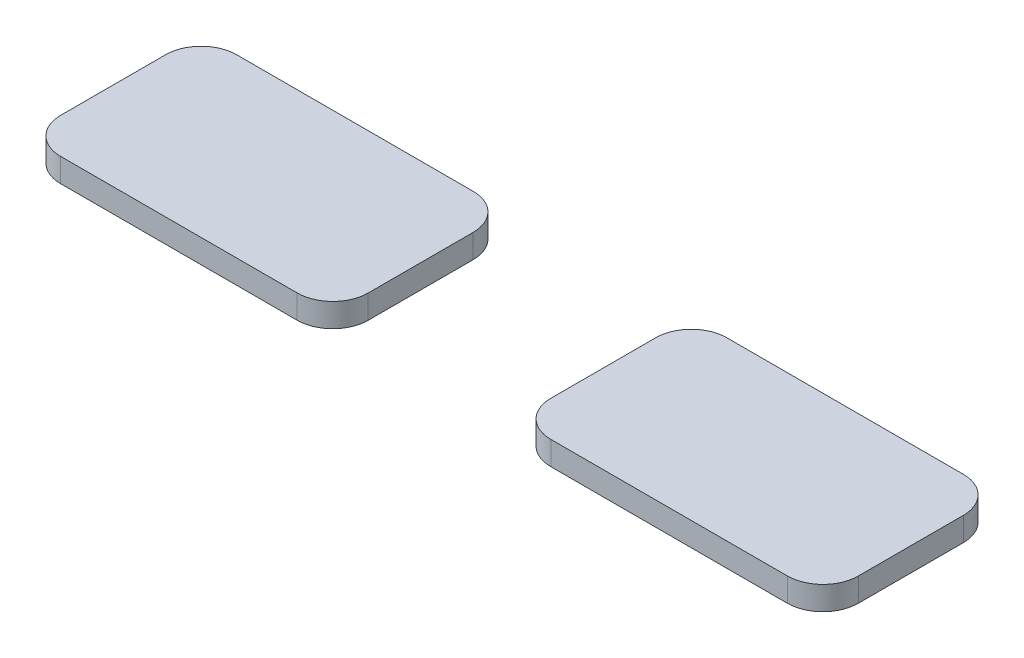
SolidWorks part; units mm, degrees
ref_plane "前视基准面" through (0, 0, 0) normal (0, 0, 1) x (1, 0, 0)
ref_plane "上视基准面" through (0, 0, 0) normal (0, 1, 0) x (1, 0, 0)
ref_plane "右视基准面" through (0, 0, 0) normal (1, 0, 0) x (0, 0, -1)
other "Configuration Table"
sketch "草图1" plane through (0, 0, 0) normal (0, 1, 0) x (1, 0, 0)
  line L0 (20.7048, 13.3126) -> (20.7048, -13.9668) construction
  line L1 (-9.995, -7.435) -> (9.995, -7.435)
  line L2 (-12.995, -4.435) -> (-12.995, 4.435)
  line L3 (-9.995, 7.435) -> (9.995, 7.435)
  line L4 (12.995, -4.435) -> (12.995, 4.435)
  line L5 (-12.995, -7.435) -> (12.995, 7.435) construction
  line L6 (-12.995, 7.435) -> (12.995, -7.435) construction
  line L7 (28.4147, -4.435) -> (28.4147, 4.435)
  line L8 (51.4047, -7.435) -> (31.4147, -7.435)
  line L9 (54.4047, -4.435) -> (54.4047, 4.435)
  line L10 (51.4047, 7.435) -> (31.4147, 7.435)
  arc A0 (9.995, 7.435) -> (12.995, 4.435) centre (9.995, 4.435) cw
  arc A1 (9.995, -7.435) -> (12.995, -4.435) centre (9.995, -4.435) ccw
  arc A2 (-9.995, -7.435) -> (-12.995, -4.435) centre (-9.995, -4.435) cw
  arc A3 (-12.995, 4.435) -> (-9.995, 7.435) centre (-9.995, 4.435) cw
  arc A4 (31.4147, 7.435) -> (28.4147, 4.435) centre (31.4147, 4.435) ccw
  arc A5 (31.4147, -7.435) -> (28.4147, -4.435) centre (31.4147, -4.435) cw
  arc A6 (51.4047, -7.435) -> (54.4047, -4.435) centre (51.4047, -4.435) ccw
  arc A7 (54.4047, 4.435) -> (51.4047, 7.435) centre (51.4047, 4.435) ccw
  point P0 (0, 0)
  dimension "D3" = 3
  dimension "D1" = 14.87
  dimension "D2" = 25.99
extrude "凸台-拉伸1" add sketch "草图1" along normal blind 2
